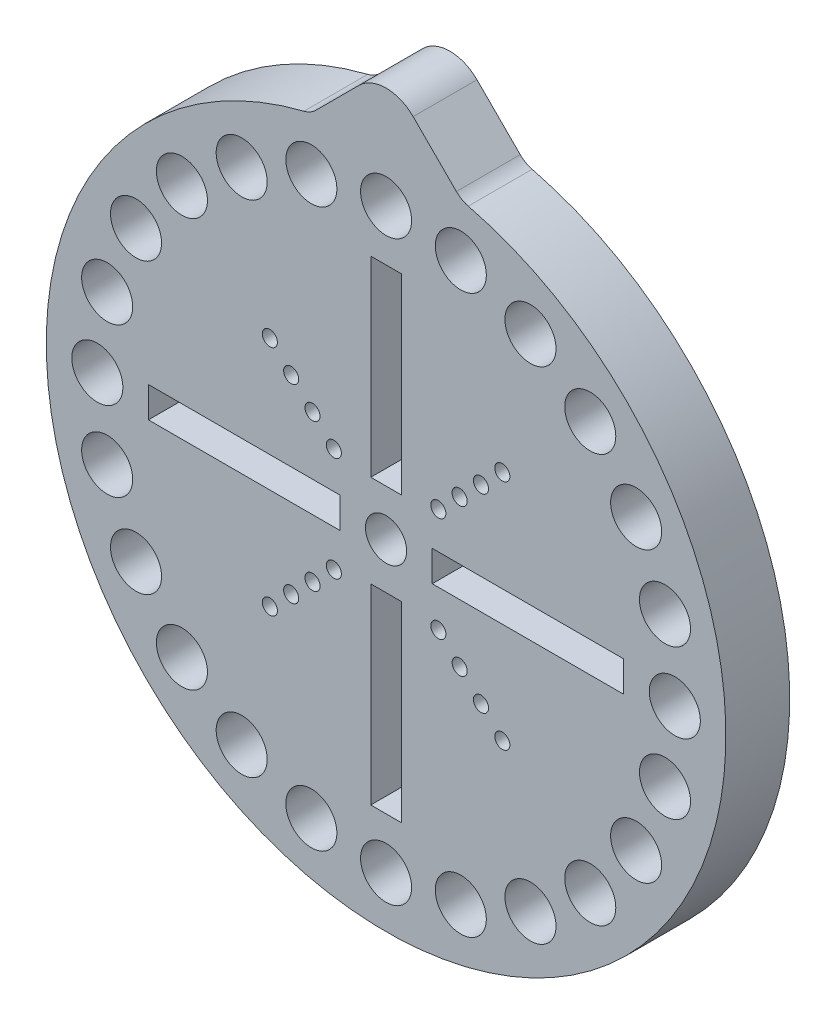
SolidWorks part; units mm, degrees
ref_plane "Front Plane" through (0, 0, 0) normal (0, 0, 1) x (1, 0, 0)
ref_plane "Top Plane" through (0, 0, 0) normal (0, 1, 0) x (1, 0, 0)
ref_plane "Right Plane" through (0, 0, 0) normal (1, 0, 0) x (0, 0, -1)
sketch "Sketch1" plane through (0, 0, 0) normal (0, 0, 1) x (1, 0, 0)
  line L0 (0, 31.26) -> (0, 33.8) construction
  line L1 (0, 28.72) -> (2.5183, 28.3885) construction
  line L2 (2.5183, 28.3885) -> (4.915, 28.0729) construction
  line L3 (4.915, 28.0729) -> (7.4333, 27.7414) construction
  line L4 (0, 2.05) -> (0, 4.59) construction
  line L5 (-0.1778, 26.1862) -> (0.1778, 26.1862) construction
  line L6 (-0.1778, 26.1862) -> (-0.1778, 30.9862) construction
  line L7 (-0.1778, 30.9862) -> (0.1778, 30.9862) construction
  line L8 (0.1778, 26.1862) -> (0.1778, 30.9862) construction
  line L9 (-1.524, 23.64) -> (1.524, 23.64)
  line L10 (-1.524, 23.64) -> (-1.524, 4.59)
  line L11 (-1.524, 4.59) -> (1.524, 4.59)
  line L12 (1.524, 23.64) -> (1.524, 4.59)
  line L13 (0, 26.18) -> (0, 23.64) construction
  line L14 (23.64, 1.524) -> (23.64, -1.524)
  line L15 (23.64, 1.524) -> (4.59, 1.524)
  line L16 (23.64, -1.524) -> (4.59, -1.524)
  line L17 (4.59, 1.524) -> (4.59, -1.524)
  line L18 (1.524, -23.64) -> (-1.524, -23.64)
  line L19 (1.524, -23.64) -> (1.524, -4.59)
  line L20 (-1.524, -23.64) -> (-1.524, -4.59)
  line L21 (1.524, -4.59) -> (-1.524, -4.59)
  line L22 (-23.64, -1.524) -> (-23.64, 1.524)
  line L23 (-23.64, -1.524) -> (-4.59, -1.524)
  line L24 (-23.64, 1.524) -> (-4.59, 1.524)
  line L25 (-4.59, -1.524) -> (-4.59, 1.524)
  line L26 (0, 0) -> (11.5612, 11.5612) construction
  line L27 (0, 0) -> (11.1701, 0) construction
  line L29 (0, 0) -> (-11.5612, 11.5612) construction
  circle A0 centre (0, 0) radius 33.8
  circle A1 centre (14.36, 24.8722) radius 2.54
  circle A2 centre (20.3081, 20.3081) radius 2.54
  circle A3 centre (24.8722, 14.36) radius 2.54
  circle A4 centre (27.7414, 7.4333) radius 2.54
  circle A5 centre (28.72, 0) radius 2.54
  circle A6 centre (27.7414, -7.4333) radius 2.54
  circle A7 centre (24.8722, -14.36) radius 2.54
  circle A8 centre (20.3081, -20.3081) radius 2.54
  circle A9 centre (14.36, -24.8722) radius 2.54
  circle A10 centre (7.4333, -27.7414) radius 2.54
  circle A11 centre (0, -28.72) radius 2.54
  circle A12 centre (-7.4333, -27.7414) radius 2.54
  circle A13 centre (-14.36, -24.8722) radius 2.54
  circle A14 centre (-20.3081, -20.3081) radius 2.54
  circle A15 centre (-24.8722, -14.36) radius 2.54
  circle A16 centre (-27.7414, -7.4333) radius 2.54
  circle A17 centre (-28.72, 0) radius 2.54
  circle A18 centre (-27.7414, 7.4333) radius 2.54
  circle A19 centre (-24.8722, 14.36) radius 2.54
  circle A20 centre (-20.3081, 20.3081) radius 2.54
  circle A21 centre (-14.36, 24.8722) radius 2.54
  circle A22 centre (-7.4333, 27.7414) radius 2.54
  circle A23 centre (0, 28.72) radius 2.54
  circle A24 centre (7.4333, 27.7414) radius 2.54
  circle A25 centre (0, 0) radius 2.05
  circle A26 centre (11.5612, 11.5612) radius 0.75
  circle A27 centre (9.4399, 9.4399) radius 0.75
  circle A28 centre (7.3186, 7.3186) radius 0.75
  circle A29 centre (5.1972, 5.1972) radius 0.75
  circle A30 centre (11.5612, -11.5612) radius 0.75
  circle A31 centre (9.4399, -9.4399) radius 0.75
  circle A32 centre (7.3186, -7.3186) radius 0.75
  circle A33 centre (5.1972, -5.1972) radius 0.75
  circle A34 centre (-11.5612, -11.5612) radius 0.75
  circle A35 centre (-9.4399, -9.4399) radius 0.75
  circle A36 centre (-7.3186, -7.3186) radius 0.75
  circle A37 centre (-5.1972, -5.1972) radius 0.75
  circle A38 centre (-11.5612, 11.5612) radius 0.75
  circle A39 centre (-9.4399, 9.4399) radius 0.75
  circle A40 centre (-7.3186, 7.3186) radius 0.75
  circle A41 centre (-5.1972, 5.1972) radius 0.75
  point P54 (0, 0)
  point P84 (0, 0)
  point P119 (0, 0)
  dimension "D1" = 5.08
  dimension "D3" = 2.54
  dimension "D5" = 4.1
  dimension "D6" = 67.6
  dimension "D4" = 3.048
  dimension "D12" = 45
  dimension "D17" = 1.5
  dimension "D18" = 4
  dimension "D8" = 4.8
  dimension "D9" = 0.3556
  dimension "D10" = 2.54
  dimension "D11" = 19.05
  dimension "D13" = 14.7
  dimension "D14" = 20.7
  dimension "D15" = 26.7
  dimension "D16" = 32.7
  dimension "D7" = 4
  dimension "D2" = 24
extrude "Boss-Extrude1" add sketch "Sketch1" along normal blind 6.35
sketch "Sketch3" plane through (0, 0, 0) normal (0, 0, 1) x (1, 0, 0)
  line L0 (0, 33.8) -> (0, 37.7641) construction
  line L1 (2.6941, 37.7641) -> (-2.6941, 37.7641) construction
  line L2 (-2.6941, 37.7641) -> (-7.501, 32.9572)
  line L3 (2.6941, 37.7641) -> (7.501, 32.9572)
  line L4 (7.501, 32.9572) -> (-7.501, 32.9572) construction
  arc A0 (2.6941, 37.7641) -> (-2.6941, 37.7641) centre (0, 35.07) ccw
  circle A1 centre (0, 0) radius 33.8
  arc A2 (7.501, 32.9572) -> (-7.501, 32.9572) centre (0, 0) ccw
  circle A3 centre (0, 0) radius 33.8 construction
  point P9 (0, 37.7641)
  dimension "D2" = 3.81
  dimension "D3" = 5.08
  dimension "D4" = 90
  dimension "D1" = 0
extrude "Boss-Extrude2" add sketch "Sketch3" along normal up to surface (6.35 mm away) up to face at (-6.5686, 7.3186, 6.35)
fillet "Fillet1" radius 2.54 2 edges at (-7.501, 32.9572, 3.175) (7.501, 32.9572, 3.175)
sketch "Sketch4" plane through (0, 0, 0) normal (0, 0, 1) x (1, 0, 0)
  line L0 (-1.397, -23.513) -> (1.397, -23.513)
  line L1 (1.397, -23.513) -> (1.397, -4.717)
  line L2 (1.397, -4.717) -> (-1.397, -4.717)
  line L3 (-1.397, -4.717) -> (-1.397, -23.513)
  line L4 (-1.524, -23.64) -> (1.524, -23.64)
  line L5 (-1.524, -4.59) -> (-1.524, -23.64)
  line L6 (1.524, -4.59) -> (-1.524, -4.59)
  line L7 (1.524, -23.64) -> (1.524, -4.59)
  line L8 (-1.524, -23.64) -> (1.524, -23.64) construction
  line L9 (-1.524, -4.59) -> (-1.524, -23.64) construction
  line L10 (1.524, -4.59) -> (-1.524, -4.59) construction
  line L11 (1.524, -23.64) -> (1.524, -4.59) construction
  line L12 (23.64, -1.524) -> (23.64, 1.524)
  line L13 (4.59, -1.524) -> (23.64, -1.524)
  line L14 (4.59, 1.524) -> (4.59, -1.524)
  line L15 (23.64, 1.524) -> (4.59, 1.524)
  line L16 (23.64, -1.524) -> (23.64, 1.524) construction
  line L17 (4.59, -1.524) -> (23.64, -1.524) construction
  line L18 (4.59, 1.524) -> (4.59, -1.524) construction
  line L19 (23.64, 1.524) -> (4.59, 1.524) construction
  line L20 (1.524, 23.64) -> (-1.524, 23.64)
  line L21 (-1.524, 23.64) -> (-1.524, 4.59)
  line L22 (-1.524, 4.59) -> (1.524, 4.59)
  line L23 (1.524, 4.59) -> (1.524, 23.64)
  line L24 (1.524, 23.64) -> (-1.524, 23.64) construction
  line L25 (-1.524, 23.64) -> (-1.524, 4.59) construction
  line L26 (-1.524, 4.59) -> (1.524, 4.59) construction
  line L27 (1.524, 4.59) -> (1.524, 23.64) construction
  line L28 (-23.64, 1.524) -> (-23.64, -1.524)
  line L29 (-4.59, 1.524) -> (-23.64, 1.524)
  line L30 (-4.59, -1.524) -> (-4.59, 1.524)
  line L31 (-23.64, -1.524) -> (-4.59, -1.524)
  line L32 (-23.64, 1.524) -> (-23.64, -1.524) construction
  line L33 (-4.59, 1.524) -> (-23.64, 1.524) construction
  line L34 (-4.59, -1.524) -> (-4.59, 1.524) construction
  line L35 (-23.64, -1.524) -> (-4.59, -1.524) construction
  line L36 (23.513, -1.397) -> (23.513, 1.397)
  line L37 (23.513, 1.397) -> (4.717, 1.397)
  line L38 (4.717, 1.397) -> (4.717, -1.397)
  line L39 (4.717, -1.397) -> (23.513, -1.397)
  line L40 (1.397, 23.513) -> (-1.397, 23.513)
  line L41 (-1.397, 23.513) -> (-1.397, 4.717)
  line L42 (-1.397, 4.717) -> (1.397, 4.717)
  line L43 (1.397, 4.717) -> (1.397, 23.513)
  line L44 (-23.513, 1.397) -> (-23.513, -1.397)
  line L45 (-23.513, -1.397) -> (-4.717, -1.397)
  line L46 (-4.717, -1.397) -> (-4.717, 1.397)
  line L47 (-4.717, 1.397) -> (-23.513, 1.397)
  circle A0 centre (0, 0) radius 33.927
  circle A1 centre (28.72, 0) radius 2.54
  circle A2 centre (28.72, 0) radius 2.54 construction
  circle A3 centre (27.7414, 7.4333) radius 2.54
  circle A4 centre (27.7414, 7.4333) radius 2.54 construction
  circle A5 centre (24.8722, 14.36) radius 2.54
  circle A6 centre (24.8722, 14.36) radius 2.54 construction
  circle A7 centre (20.3081, 20.3081) radius 2.54
  circle A8 centre (20.3081, 20.3081) radius 2.54 construction
  circle A9 centre (14.36, 24.8722) radius 2.667
  circle A10 centre (14.36, 24.8722) radius 2.667 construction
  circle A11 centre (0, 0) radius 33.8
  circle A12 centre (0, 0) radius 33.8 construction
  circle A13 centre (-14.36, -24.8722) radius 2.54
  circle A14 centre (-14.36, -24.8722) radius 2.54 construction
  circle A15 centre (-7.4333, -27.7414) radius 2.54
  circle A16 centre (-7.4333, -27.7414) radius 2.54 construction
  circle A17 centre (0, -28.72) radius 2.54
  circle A18 centre (0, -28.72) radius 2.54 construction
  circle A19 centre (7.4333, -27.7414) radius 2.54
  circle A20 centre (7.4333, -27.7414) radius 2.54 construction
  circle A21 centre (14.36, -24.8722) radius 2.54
  circle A22 centre (14.36, -24.8722) radius 2.54 construction
  circle A23 centre (20.3081, -20.3081) radius 2.54
  circle A24 centre (20.3081, -20.3081) radius 2.54 construction
  circle A25 centre (24.8722, -14.36) radius 2.54
  circle A26 centre (24.8722, -14.36) radius 2.54 construction
  circle A27 centre (27.7414, -7.4333) radius 2.54
  circle A28 centre (27.7414, -7.4333) radius 2.54 construction
  circle A29 centre (-14.36, 24.8722) radius 2.54
  circle A30 centre (-14.36, 24.8722) radius 2.54 construction
  circle A31 centre (-20.3081, 20.3081) radius 2.54
  circle A32 centre (-20.3081, 20.3081) radius 2.54 construction
  circle A33 centre (-24.8722, 14.36) radius 2.54
  circle A34 centre (-24.8722, 14.36) radius 2.54 construction
  circle A35 centre (-27.7414, 7.4333) radius 2.54
  circle A36 centre (-27.7414, 7.4333) radius 2.54 construction
  circle A37 centre (-28.72, 0) radius 2.54
  circle A38 centre (-28.72, 0) radius 2.54 construction
  circle A39 centre (-27.7414, -7.4333) radius 2.54
  circle A40 centre (-27.7414, -7.4333) radius 2.54 construction
  circle A41 centre (-24.8722, -14.36) radius 2.54
  circle A42 centre (-24.8722, -14.36) radius 2.54 construction
  circle A43 centre (-20.3081, -20.3081) radius 2.54
  circle A44 centre (-20.3081, -20.3081) radius 2.54 construction
  circle A45 centre (0, 0) radius 2.05
  circle A46 centre (0, 0) radius 2.05 construction
  circle A47 centre (7.4333, 27.7414) radius 2.54
  circle A48 centre (7.4333, 27.7414) radius 2.54 construction
  circle A49 centre (0, 28.72) radius 2.54
  circle A50 centre (0, 28.72) radius 2.54 construction
  circle A51 centre (-7.4333, 27.7414) radius 2.54
  circle A52 centre (-7.4333, 27.7414) radius 2.54 construction
  circle A53 centre (28.72, 0) radius 2.413
  circle A54 centre (27.7414, 7.4333) radius 2.413
  circle A55 centre (24.8722, 14.36) radius 2.413
  circle A56 centre (20.3081, 20.3081) radius 2.413
  circle A57 centre (14.36, 24.8722) radius 2.54 construction
  circle A58 centre (-14.36, -24.8722) radius 2.413
  circle A59 centre (-7.4333, -27.7414) radius 2.413
  circle A60 centre (0, -28.72) radius 2.413
  circle A61 centre (7.4333, -27.7414) radius 2.413
  circle A62 centre (14.36, -24.8722) radius 2.413
  circle A63 centre (20.3081, -20.3081) radius 2.413
  circle A64 centre (24.8722, -14.36) radius 2.413
  circle A65 centre (27.7414, -7.4333) radius 2.413
  circle A66 centre (-14.36, 24.8722) radius 2.413
  circle A67 centre (-20.3081, 20.3081) radius 2.413
  circle A68 centre (-24.8722, 14.36) radius 2.413
  circle A69 centre (-27.7414, 7.4333) radius 2.413
  circle A70 centre (-28.72, 0) radius 2.413
  circle A71 centre (-27.7414, -7.4333) radius 2.413
  circle A72 centre (-24.8722, -14.36) radius 2.413
  circle A73 centre (-20.3081, -20.3081) radius 2.413
  circle A74 centre (0, 0) radius 1.923
  circle A75 centre (7.4333, 27.7414) radius 2.413
  circle A76 centre (0, 28.72) radius 2.413
  circle A77 centre (-7.4333, 27.7414) radius 2.413
  circle A78 centre (14.36, 24.8722) radius 2.413
  circle A79 centre (-5.1972, -5.1972) radius 0.75 construction
  circle A80 centre (-7.3186, -7.3186) radius 0.75 construction
  circle A81 centre (-9.4399, -9.4399) radius 0.75 construction
  circle A82 centre (-11.5612, -11.5612) radius 0.75 construction
  circle A83 centre (5.1972, -5.1972) radius 0.75 construction
  circle A84 centre (7.3186, -7.3186) radius 0.75 construction
  circle A85 centre (9.4399, -9.4399) radius 0.75 construction
  circle A86 centre (11.5612, -11.5612) radius 0.75 construction
  circle A87 centre (11.5612, 11.5612) radius 0.75 construction
  circle A88 centre (9.4399, 9.4399) radius 0.75 construction
  circle A89 centre (7.3186, 7.3186) radius 0.75 construction
  circle A90 centre (5.1972, 5.1972) radius 0.75 construction
  circle A91 centre (-5.1972, 5.1972) radius 0.75 construction
  circle A92 centre (-7.3186, 7.3186) radius 0.75 construction
  circle A93 centre (-9.4399, 9.4399) radius 0.75 construction
  circle A94 centre (-11.5612, 11.5612) radius 0.75 construction
  circle A95 centre (-5.1972, -5.1972) radius 0.75 construction
  circle A96 centre (-7.3186, -7.3186) radius 0.75 construction
  circle A97 centre (-9.4399, -9.4399) radius 0.75 construction
  circle A98 centre (-11.5612, -11.5612) radius 0.75 construction
  circle A99 centre (5.1972, -5.1972) radius 0.75 construction
  circle A100 centre (7.3186, -7.3186) radius 0.75 construction
  circle A101 centre (9.4399, -9.4399) radius 0.75 construction
  circle A102 centre (11.5612, -11.5612) radius 0.75 construction
  circle A103 centre (11.5612, 11.5612) radius 0.75 construction
  circle A104 centre (9.4399, 9.4399) radius 0.75 construction
  circle A105 centre (7.3186, 7.3186) radius 0.75 construction
  circle A106 centre (5.1972, 5.1972) radius 0.75 construction
  circle A107 centre (-5.1972, 5.1972) radius 0.75 construction
  circle A108 centre (-7.3186, 7.3186) radius 0.75 construction
  circle A109 centre (-9.4399, 9.4399) radius 0.75 construction
  circle A110 centre (-11.5612, 11.5612) radius 0.75 construction
  circle A111 centre (11.5612, 11.5612) radius 0.623
  circle A112 centre (9.4399, 9.4399) radius 0.623
  circle A113 centre (7.3186, 7.3186) radius 0.623
  circle A114 centre (5.1972, 5.1972) radius 0.623
  circle A115 centre (-5.1972, 5.1972) radius 0.623
  circle A116 centre (-7.3186, 7.3186) radius 0.623
  circle A117 centre (-9.4399, 9.4399) radius 0.623
  circle A118 centre (-11.5612, 11.5612) radius 0.623
  circle A119 centre (5.1972, -5.1972) radius 0.623
  circle A120 centre (7.3186, -7.3186) radius 0.623
  circle A121 centre (9.4399, -9.4399) radius 0.623
  circle A122 centre (11.5612, -11.5612) radius 0.623
  circle A123 centre (-5.1972, -5.1972) radius 0.623
  circle A124 centre (-7.3186, -7.3186) radius 0.623
  circle A125 centre (-9.4399, -9.4399) radius 0.623
  circle A126 centre (-11.5612, -11.5612) radius 0.623
  dimension "D1" = 0
  dimension "D2" = 0
  dimension "D3" = 0
  dimension "D4" = 0
  dimension "D5" = 0.127
  dimension "D6" = 0
  dimension "D7" = 0
  dimension "D8" = 0
  dimension "D9" = 0
  dimension "D10" = 0
  dimension "D11" = 0
  dimension "D12" = 0
  dimension "D13" = 0
  dimension "D14" = 0
  dimension "D15" = 0
  dimension "D16" = 0
  dimension "D17" = 0
  dimension "D18" = 0
  dimension "D19" = 0
  dimension "D20" = 0
  dimension "D21" = 0
  dimension "D22" = 0
  dimension "D23" = 0
  dimension "D24" = 0
  dimension "D25" = 0
  dimension "D26" = 0
  dimension "D27" = 0
  dimension "D28" = 0
  dimension "D29" = 0
  dimension "D30" = 0
  dimension "D31" = 0.127
  dimension "D32" = 0.127
  dimension "D33" = 0.127
  dimension "D34" = 0.127
extrude "Kerf Adjustment" [suppressed] add sketch "Sketch4" along normal up to surface (6.35 mm away)
equation "\"kerf_adjustment\"=0.005"
equation "\"D32@Sketch4\"= \"kerf_adjustment\""
equation "\"D31@Sketch4\" = \"kerf_adjustment\""
equation "\"D33@Sketch4\"= \"kerf_adjustment\""
